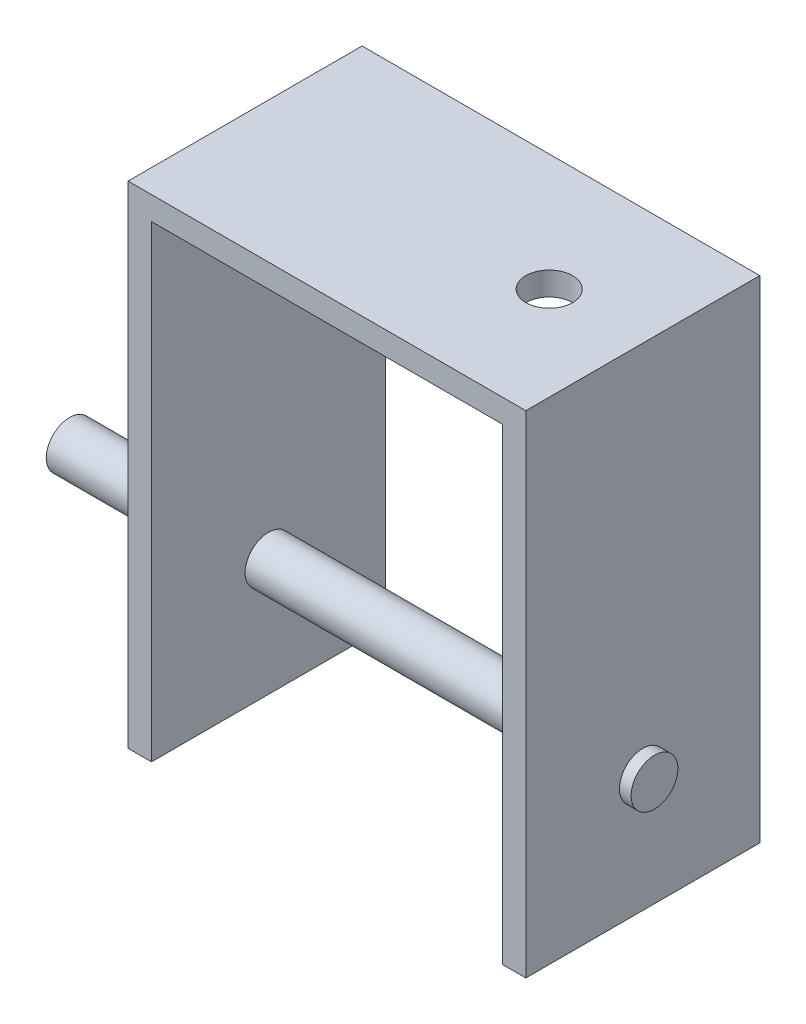
SolidWorks part; units mm, degrees
ref_plane "前视基准面" through (0, 0, 0) normal (0, 0, 1) x (1, 0, 0)
ref_plane "上视基准面" through (0, 0, 0) normal (0, 1, 0) x (1, 0, 0)
ref_plane "右视基准面" through (0, 0, 0) normal (1, 0, 0) x (0, 0, -1)
sketch "草图1" plane through (0, 0, 0) normal (0, 0, 1) x (1, 0, 0)
  line L0 (-38.9637, 28.8454) -> (-38.9637, -11.1546)
  line L1 (-38.9637, -11.1546) -> (-36.9637, -11.1546)
  line L2 (-36.9637, -11.1546) -> (-36.9637, 28.8454)
  line L3 (-36.9637, 28.8454) -> (-6.9637, 28.8454)
  line L4 (-6.9637, 28.8454) -> (-6.9637, -11.1546)
  line L5 (-6.9637, -11.1546) -> (-4.9637, -11.1546)
  line L6 (-4.9637, -11.1546) -> (-4.9637, 30.8454)
  line L7 (-4.9637, 30.8454) -> (-38.9637, 30.8454)
  line L8 (-38.9637, 30.8454) -> (-38.9637, 28.8454)
  dimension "D1" = 40
  dimension "D2" = 2
  dimension "D3" = 30
  dimension "D4" = 2
  dimension "D5" = 42
extrude "凸台-拉伸1" add sketch "草图1" along normal blind 20
sketch "草图3" plane through (-38.9637, 0, 0) normal (-1, 0, 0) x (0, 0, 1)
  line L0 (10, 30.8454) -> (10, -11.1546) construction
  line L1 (20, 30.8454) -> (0, 30.8454) construction
  line L2 (20, -11.1546) -> (0, -11.1546) construction
  line L3 (10, -11.1546) -> (10, -1.1546) construction
  circle A1 centre (10, -1.1546) radius 2
  dimension "D1" = 10
  dimension "D2" = 4
extrude "凸台-拉伸2" add sketch "草图3" along normal blind 15 and the other way blind 35
sketch "草图4" plane through (0, 30.8454, 0) normal (0, 1, 0) x (1, 0, 0)
  line L0 (-38.9637, -10) -> (-12.9637, -10) construction
  line L1 (-38.9637, -20) -> (-38.9637, 0) construction
  circle A0 centre (-12.9637, -10) radius 2
  dimension "D2" = 4
  dimension "D1" = 26
extrude "切除-拉伸1" cut sketch "草图4" against normal blind 2
